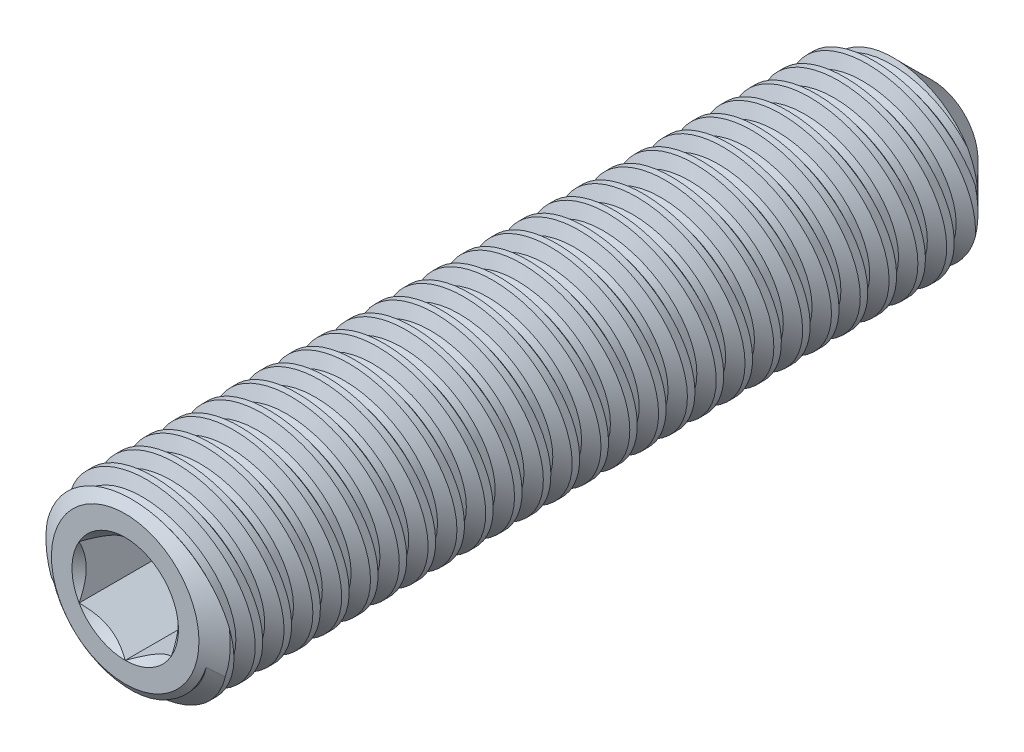
SolidWorks part; units mm, degrees
material "Plain Carbon Steel"
ref_plane "Front" through (0, 0, 0) normal (0, 0, 1) x (1, 0, 0)
ref_plane "Top" through (0, 0, 0) normal (0, 1, 0) x (1, 0, 0)
ref_plane "Right" through (0, 0, 0) normal (1, 0, 0) x (0, 0, -1)
sketch "Sketch22" plane through (0, 0, 0) normal (1, 0, 0) x (0, 0, -1)
  line L0 (-16.8991, 0) -> (-16.8991, 3.2)
  line L1 (-16.8991, 3.2) -> (-16.339, 4)
  line L2 (-16.339, 4) -> (16.1009, 4)
  line L3 (16.1009, 4) -> (18.1009, 2)
  line L4 (18.1009, 2) -> (16.8991, 0)
  line L5 (16.8991, 0) -> (-16.8991, 0)
  line L6 (16.8991, 0) -> (18.1009, 0) construction
  line L7 (18.1009, 0) -> (18.1009, 2) construction
  line L8 (18.1009, -2) -> (16.8991, 0) construction
  line L9 (-16.339, -4) -> (16.1009, -4) construction
  dimension "Screw Dia" = 8
  dimension "Length" = 35
  dimension "D3" = 35
  dimension "Cup Point Dia" = 4
  dimension "D5" = 118
  dimension "D6" = 45
  dimension "D7" = 6.4
revolve "Revolve1" add sketch "Sketch22" angle 360 about L6
sketch "Sketch6" plane through (0, 0, 0) normal (1, 0, 0) x (0, 0, -1)
  line L0 (14.1392, 4) -> (15.3892, -4) construction
  line L1 (-16.339, 4) -> (16.1009, 4) construction
  line L2 (-16.339, -4) -> (16.1009, -4) construction
  line L3 (14.1392, 4) -> (14.2936, 4.0241) construction
  line L4 (15.0927, 3.4642) -> (14.784, 3.416)
  line L5 (14.784, 3.416) -> (14.2936, 4.0241)
  line L6 (15.0927, 3.4642) -> (15.3742, 4.193)
  line L7 (15.3742, 4.193) -> (14.2936, 4.0241)
  line L8 (14.8509, 4) -> (16.1009, -4) construction
  line L9 (16.8125, 0.2089) -> (14.1392, -0.2089) construction
  line L10 (14.8339, 4.1085) -> (14.9383, 3.4401) construction
  line L13 (14.1392, -4) -> (14.1392, 4) construction
  line L14 (14.1392, -4) -> (15.3892, -4) construction
  line L15 (15.3892, -4) -> (16.1009, -4) construction
  line L18 (14.1392, 4) -> (14.8509, 4) construction
  point P18 (15.4759, 0)
  dimension "D1" = 1.25
  dimension "D2" = 0.3125
  dimension "D3" = 60
  dimension "D4" = 0.1562
  dimension "Pitch" = 1.25
revolve "Cut-Revolve8" cut sketch "Sketch6" angle 360 about L9
pattern_linear "LPattern1" count 27 spacing 1.25 along (0, 0, 1) count 2 spacing 1.25 along (0, 0, -1) of "Cut-Revolve8"
sketch "Sketch23" plane through (0, 0, 16.8991) normal (0, 0, 1) x (1, 0, 0)
  line L1 (0, 2.3094) -> (-2, 1.1547)
  line L2 (-2, 1.1547) -> (-2, -1.1547)
  line L3 (-2, -1.1547) -> (0, -2.3094)
  line L4 (0, -2.3094) -> (2, -1.1547)
  line L5 (2, -1.1547) -> (2, 1.1547)
  line L6 (2, 1.1547) -> (0, 2.3094)
  circle A0 centre (0, 0) radius 2 construction
  dimension "Hex" = 4
extrude "Cut-Extrude10" cut sketch "Sketch23" against normal blind 4
sketch "Sketch24" plane through (0, 0, 16.8991) normal (0, 0, 1) x (1, 0, 0)
  circle A0 centre (0, 0) radius 2.3094
extrude "Cut-Extrude11" cut sketch "Sketch24" against normal through all draft 45
sketch "Sketch26" plane through (0, 0, 12.8991) normal (0, 0, 1) x (1, 0, 0)
  circle A0 centre (0, 0) radius 2 construction
  circle A1 centre (0, 0) radius 2
extrude "Cut-Extrude12" cut sketch "Sketch26" against normal through all draft 59
equation "\"D2@Sketch6\"=\"Pitch@Sketch6\"/4"
equation "\"D4@Sketch6\"=\"Pitch@Sketch6\"/8"
equation "\"D1@Sketch6\"=\"Pitch@Sketch6\""
equation "\"D3@LPattern1\"=\"Pitch@Sketch6\""
equation "\"D1@LPattern1\"=(\"Length@Sketch22\"/\"Pitch@Sketch6\")-1"
equation "\"D4@LPattern1\"=\"Pitch@Sketch6\""
equation "\"D7@Sketch22\"=\"Screw Dia@Sketch22\"*.8"
